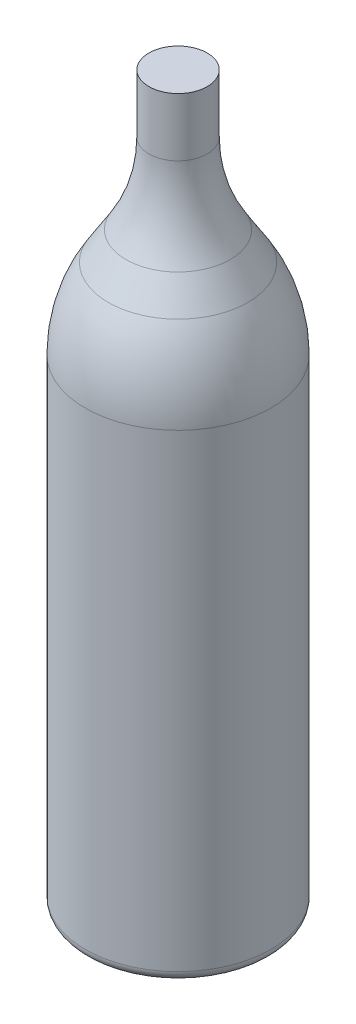
SolidWorks part; units mm, degrees
ref_plane "Front Plane" through (0, 0, 0) normal (0, 0, 1) x (1, 0, 0)
ref_plane "Top Plane" through (0, 0, 0) normal (0, 1, 0) x (1, 0, 0)
ref_plane "Right Plane" through (0, 0, 0) normal (1, 0, 0) x (0, 0, -1)
sketch "Sketch2" plane through (0, 0, 0) normal (0, 0, 1) x (1, 0, 0)
  line L0 (0, 0) -> (0, 274) construction
  line L1 (0, 274) -> (-11, 274)
  line L2 (-11, 274) -> (-11, 252)
  line L3 (-19.6613, 221.7946) -> (-26.3387, 211.1084)
  line L4 (-35, 180.903) -> (-35, 4)
  line L5 (-31, 0) -> (-29, 0)
  line L6 (-18.5772, 5.2306) -> (-8.3619, 18.9345)
  line L7 (0, 22.4566) -> (0, 274)
  arc A0 (-26.3387, 211.1084) -> (-35, 180.903) centre (22, 180.903) ccw
  arc A1 (-11, 252) -> (-19.6613, 221.7946) centre (-68, 252) cw
  arc A2 (-31, 0) -> (-35, 4) centre (-31, 4) cw
  arc A3 (-18.5772, 5.2306) -> (-29, 0) centre (-29, 13) cw
  arc A4 (-8.3619, 18.9345) -> (0, 22.4566) centre (0, 10.7696) cw
  point P9 (0, 274)
  point P10 (0, 274)
  point P15 (0, 274)
  point P16 (0, 0)
  dimension "D5" = 57
  dimension "D7" = 4
  dimension "D8" = 13
  dimension "D1" = 274
  dimension "D2" = 11
  dimension "D3" = 35
  dimension "D4" = 148
  dimension "D6" = 22
  dimension "D9" = 6
revolve "Revolve1" add sketch "Sketch2" angle 360 about L0
